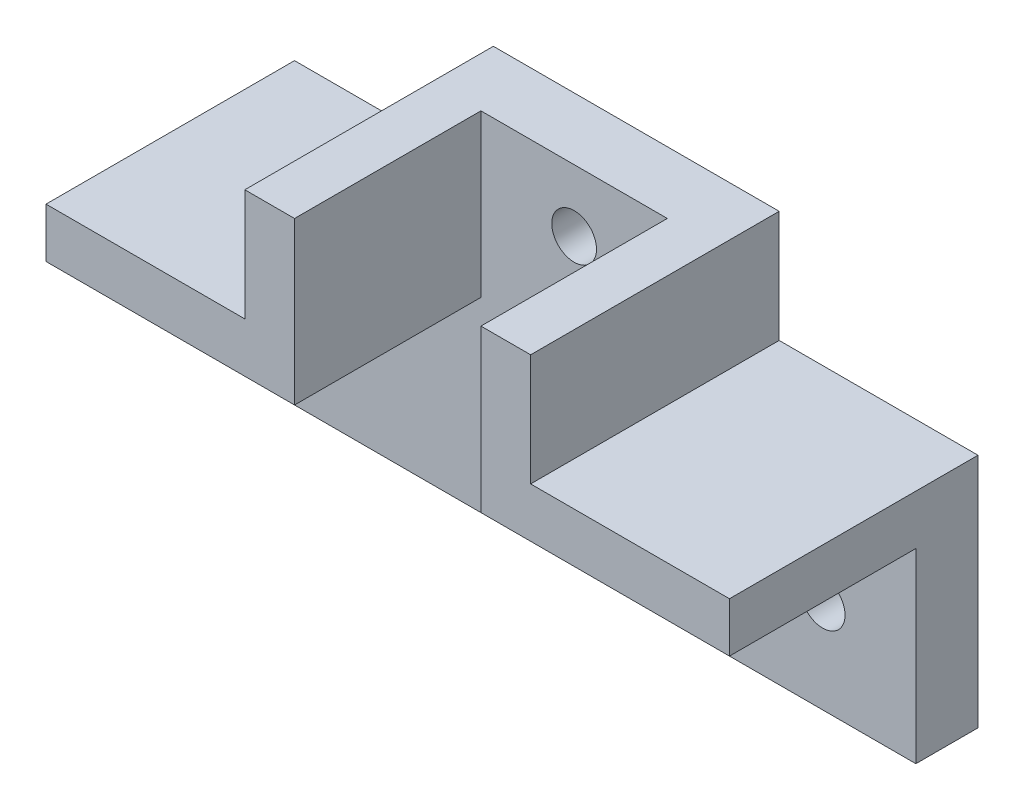
SolidWorks part; units mm, degrees
ref_plane "Front Plane" through (0, 0, 0) normal (0, 0, 1) x (1, 0, 0)
ref_plane "Top Plane" through (0, 0, 0) normal (0, 1, 0) x (1, 0, 0)
ref_plane "Right Plane" through (0, 0, 0) normal (1, 0, 0) x (0, 0, -1)
sketch "Sketch1" plane through (0, 0, 0) normal (0, 0, 1) x (1, 0, 0)
  line L0 (14.3137, 2.7353) -> (34.3137, 2.7353)
  line L1 (-20.6863, 2.7353) -> (-0.6863, 2.7353)
  line L2 (-20.6863, 2.7353) -> (-20.6863, -12.2647)
  line L3 (-20.6863, -12.2647) -> (34.3137, -12.2647)
  line L4 (34.3137, 2.7353) -> (34.3137, -12.2647)
  line L5 (-0.6863, 15.7353) -> (14.3137, 15.7353)
  line L6 (-0.6863, 15.7353) -> (-0.6863, 2.7353)
  line L8 (14.3137, 15.7353) -> (14.3137, 2.7353)
  dimension "D1" = 15
  dimension "D2" = 13
  dimension "D3" = 20
  dimension "D4" = 15
  dimension "D5" = 20
extrude "Boss-Extrude1" add sketch "Sketch1" along normal blind 5
sketch "Sketch2" plane through (0, 0, 0) normal (0, 0, -1) x (-1, 0, 0)
  line L0 (0.6863, 15.7353) -> (4.6863, 15.7353)
  line L1 (4.6863, 15.7353) -> (4.6863, 6.7353)
  line L2 (20.6863, 2.7353) -> (20.6863, 6.7353)
  line L3 (20.6863, 6.7353) -> (6.08, 6.7353)
  line L4 (20.6863, 2.7353) -> (0.6863, 2.7353)
  line L5 (0.6863, 15.7353) -> (0.6863, 2.7353)
  line L6 (6.08, 6.7353) -> (4.6863, 6.7353)
  dimension "D1" = 4
  dimension "D2" = 4
extrude "Boss-Extrude2" add sketch "Sketch2" against normal blind 20 contours L3 L6 L1 L0 L5 L4 L2
ref_plane "Plane4" through (6.8137, 0, 0) normal (-1, 0, 0) x (0, 0, 1)
ref_plane "Plane5" through (-5.6863, 0, 0) normal (-1, 0, 0) x (0, 0, 1)
mirror "Mirror1" about plane through (6.8137, 0, 0) normal (-1, 0, 0) of "Boss-Extrude2"
sketch "Sketch6" plane through (0, 0, 5) normal (0, 0, 1) x (1, 0, 0)
  line L0 (6.8137, 3.3) -> (6.8137, -3.3) construction
  line L1 (-20.6863, 2.7353) -> (-20.6863, -12.2647) construction
  line L2 (-20.6863, 2.7353) -> (-0.6863, 2.7353) construction
  line L3 (34.3137, 2.7353) -> (14.3137, 2.7353) construction
  line L5 (34.3137, -12.2647) -> (34.3137, 2.7353) construction
  line L6 (14.3137, 15.7353) -> (-0.6863, 15.7353) construction
  circle A0 centre (6.8137, 10.7353) radius 1.8
  circle A1 centre (-13.1863, -4.7647) radius 1.8
  circle A2 centre (26.8137, -4.7647) radius 1.8
  dimension "D1" = 3.6
  dimension "D2" = 3.6
  dimension "D3" = 3.6
  dimension "D5" = 7.5
  dimension "D7" = 7.5
  dimension "D8" = 5
  dimension "D4" = 7.5
  dimension "D6" = 7.5
ref_plane "Plane6" through (-4.6863, 6.7353, 20) normal (0, -1, 0) x (-1, 0, 0)
extrude "Cut-Extrude3" cut sketch "Sketch6" against normal through all
